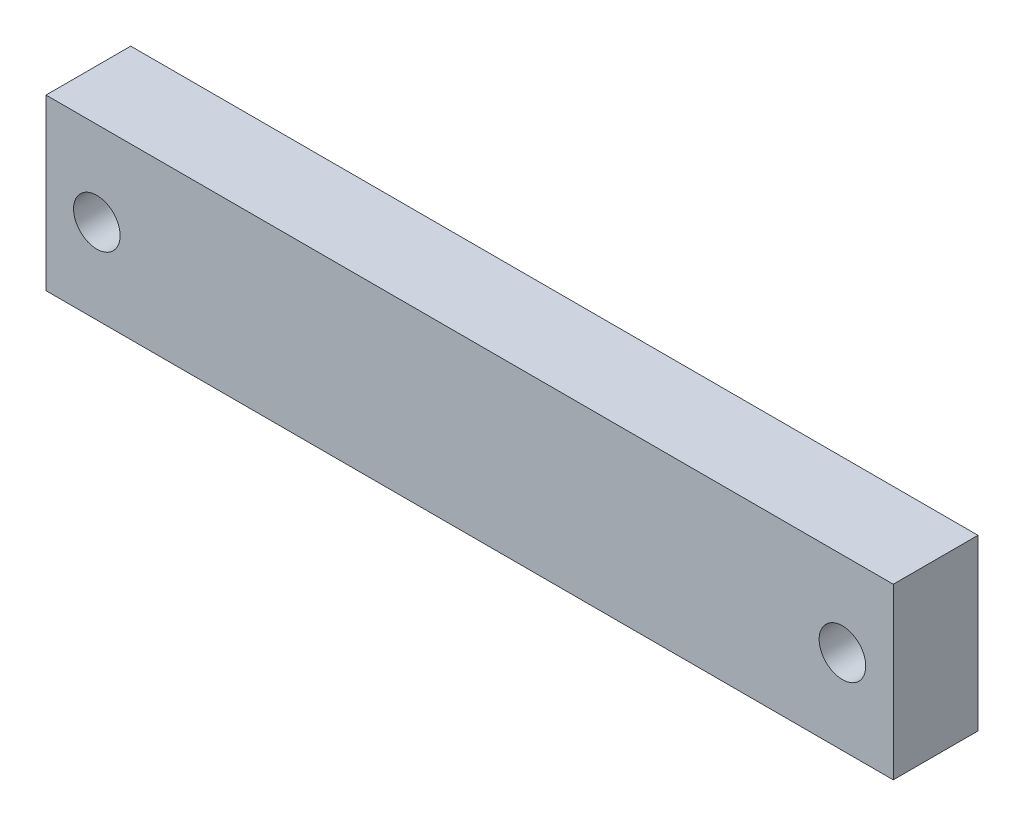
SolidWorks part; units mm, degrees
ref_plane "Front Plane" through (0, 0, 0) normal (0, 0, 1) x (1, 0, 0)
ref_plane "Top Plane" through (0, 0, 0) normal (0, 1, 0) x (1, 0, 0)
ref_plane "Right Plane" through (0, 0, 0) normal (1, 0, 0) x (0, 0, -1)
ref_plane "Plane1" through (0, 0, 10) normal (0, 0, 1) x (1, 0, 0)
sketch "Sketch1" plane through (0, 0, 10) normal (0, 0, 1) x (1, 0, 0)
  line L0 (0, 20) -> (0, 0)
  line L1 (0, 0) -> (100, 0)
  line L2 (100, 0) -> (100, 20)
  line L3 (100, 20) -> (0, 20)
extrude "Boss-Extrude1" add sketch "Sketch1" against normal blind 10
sketch "Sketch2" plane through (0, 0, 10) normal (0, 0, 1) x (1, 0, 0)
  circle A0 centre (94, 10) radius 2.75
  circle A1 centre (6, 10) radius 2.75
extrude "Cut-Extrude1" cut sketch "Sketch2" against normal through all
